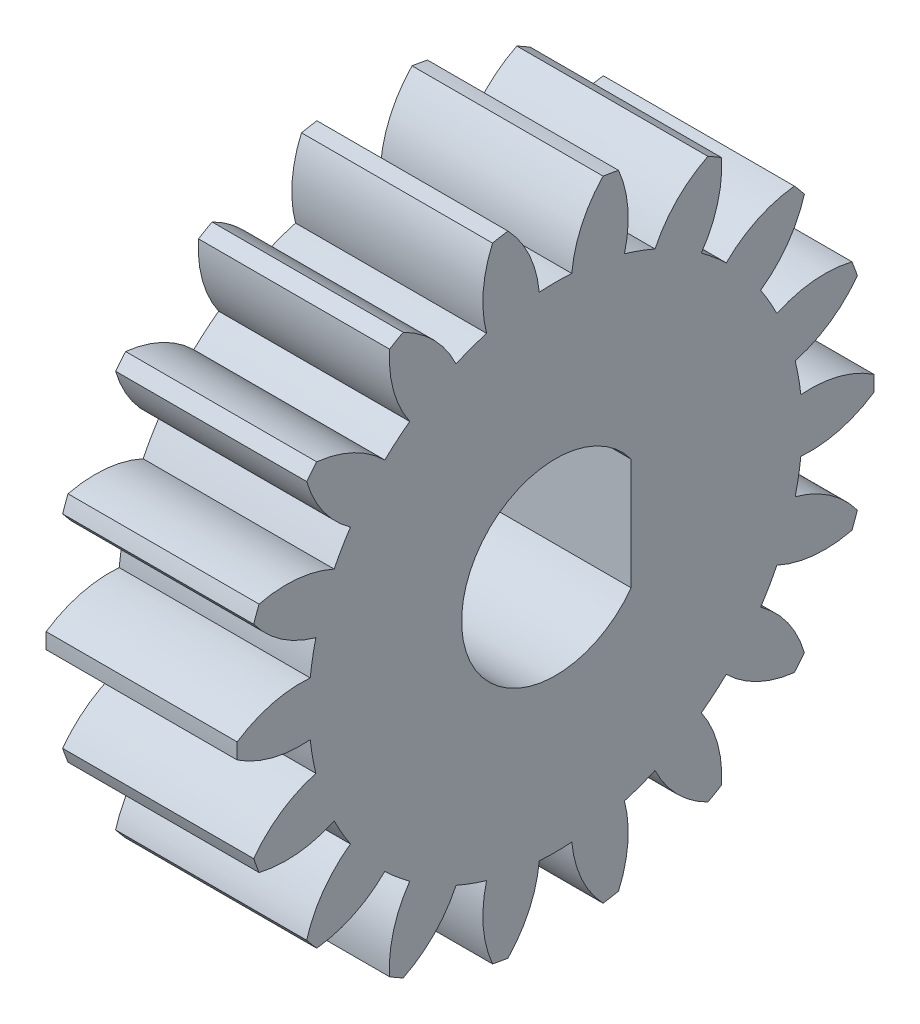
SolidWorks part; units mm, degrees
ref_plane "Plane1" through (0, 0, 0) normal (0, 0, 1) x (1, 0, 0)
ref_plane "Plane2" through (0, 0, 0) normal (0, 1, 0) x (1, 0, 0)
ref_plane "Plane3" through (0, 0, 0) normal (1, 0, 0) x (0, 0, -1)
sketch "HoldingSke" plane through (0, 0, 0) normal (0, 1, 0) x (1, 0, 0)
  line L0 (0, 0) -> (0.9511, -0.309)
  line L1 (-15, 0) -> (100, 0) construction
  line L2 (0, 0) -> (-2.1039, 2.3779)
  line L3 (0, 0) -> (-11.863, 4.5341)
  line L4 (0, 0) -> (8.2133, 2.6687)
  line L5 (0, 0) -> (-46.8476, -17.4728)
  line L6 (0, 0) -> (-4.9738, -3.3558)
  line L7 (-2.1039, 2.3779) -> (8.6586, 51.206)
  line L8 (-76.2, 54.61) -> (-75.2, 54.61)
  line L9 (-71.009, 38.7566) -> (-53.1078, 45.2721)
  line L10 (-76.2, 71.12) -> (104.1128, 71.12)
  line L11 (0, 0) -> (-6, 0)
  line L12 (-76.2, 101.6) -> (-76.162, 101.6)
  line L13 (24.9733, 27.94) -> (52.9518, 28.4284)
  line L14 (24.9733, 27.94) -> (24.9743, 27.94)
  line L15 (24.9733, 27.94) -> (100.4006, 29.5858)
  line L16 (-63.627, -1) -> (-12.827, -1)
  circle A0 centre (0, 0) radius 3
  circle A1 centre (0, 0) radius 7.749
  circle A2 centre (0, 0) radius 37.5
  circle A3 centre (0, 0) radius 3
  dimension "MHD" = 15.498
  dimension "Hub_dia" = 75
  dimension "Bore" = 6
  dimension "MBD" = 6
  dimension "Num_teeth" = 18
  dimension "Pitch" = 1
  dimension "Overall_len" = 50
  dimension "Show_teeth" = 18
  dimension "Thickness" = 6
  dimension "OAL" = 50.0002
  dimension "T_dim" = 1
  dimension "Ap" = 20
  dimension "H" = 19.05
  dimension "Pitch_radius" = 180.3128
  dimension "Width" = 6
  dimension "Backlash" = 0.038
  dimension "Addendum_fac" = 1
  dimension "Dedendum_fac" = 1.25
  dimension "Clearance_fac" = 0.25
  dimension "Dedendum_add" = 0.001
  dimension "Module" = 1
sketch "BasProSke" plane through (0, 0, 0) normal (0, 1, 0) x (1, 0, 0)
  line L0 (-10, 0) -> (60, 0) construction
  line L1 (0, 0) -> (0, 10)
  line L2 (0, 0) -> (6, 0)
  line L3 (6, 0) -> (6, 10)
  line L4 (6, 10) -> (0, 10)
  dimension "Thickness" = 6
  dimension "Diameter" = 20
revolve "Base-Revolve" add sketch "BasProSke" angle 360 about L0
sketch "TooCutSke" plane through (0, 0, 0) normal (1, 0, 0) x (0, 0, -1)
  line L1 (0, 0) -> (0, 107) construction
  line L2 (0, 0) -> (-0.8509, 8.9597) construction
  line L3 (0, 0) -> (-3.1157, 17.6701) construction
  line L4 (-0.8509, 8.9597) -> (-1.5579, 8.835) construction
  arc A0 (0.5106, 7.7322) -> (-0.5106, 7.7322) centre (0, 0) ccw
  arc A1 (1.5152, 9.9102) -> (-1.5152, 9.9102) centre (0, 0) ccw
  circle A2 centre (0, 0) radius 9 construction
  circle A3 centre (0, 0) radius 8.4572 construction
  arc A4 (-0.5106, 7.7322) -> (-1.5152, 9.9102) centre (-4.0952, 7.3996) ccw
  arc A5 (1.5152, 9.9102) -> (0.5106, 7.7322) centre (4.0952, 7.3996) ccw
  dimension "Root_dia" = 15.498
  dimension "Overcut_dia" = 20.0508
  dimension "Pitch_dia" = 18
  dimension "Base_dia" = 16.9145
  dimension "Flank_rad" = 3.6
  dimension "Half_ang" = 10
  dimension "Half_CT" = 0.7179
extrude "ToothCut" cut sketch "TooCutSke" along normal through all
fillet "Breaks" [suppressed] radius 0.02
fillet "RootFillets" [suppressed] radius 0.251
pattern_circular "TeethCuts" count 18 every 20 about axis through (-10, 0, 0) along (1, 0, 0) of "ToothCut", "RootFillets", "Breaks"
sketch "HubNeaOneSke" plane through (0, 0, 0) normal (-1, 0, 0) x (0, 0, 1)
  circle A0 centre (0, 0) radius 7.749
  dimension "Diameter" = 15.498
extrude "HubNearOne" [suppressed] add sketch "HubNeaOneSke" along normal blind 44.0002
sketch "HubNeaBotSke" plane through (0, 0, 0) normal (-1, 0, 0) x (0, 0, 1)
  circle A0 centre (0, 0) radius 7.749
  dimension "Diameter" = 15.498
extrude "HubNearBoth" [suppressed] add sketch "HubNeaBotSke" along normal blind 22.0001
ref_plane "FarPln" through (6, 0, 0) normal (1, 0, 0) x (0, 0, -1)
sketch "HubFarSke" plane through (6, 0, 0) normal (1, 0, 0) x (0, 0, -1)
  circle A0 centre (0, 0) radius 7.749
  dimension "Diameter" = 15.498
extrude "HubFar" [suppressed] add sketch "HubFarSke" along normal blind 22.0001
sketch "KeySke" plane through (0, 0, 0) normal (1, 0, 0) x (0, 0, -1)
  line L0 (-1, 0) -> (-1, 4)
  line L1 (-1, 4) -> (1, 4)
  line L2 (1, 4) -> (1, 0)
  line L3 (0, 0) -> (0, 34) construction
  line L4 (-1, 0) -> (1, 0)
  dimension "Offset" = 4
  dimension "Width" = 2
extrude "Keyway" [suppressed] cut sketch "KeySke" along normal mid plane 100.0003
pattern_circular "Keyway2" [suppressed] count 2 every 90 about axis through (-10, 0, 0) along (1, 0, 0)
sketch "Sketch1" plane through (6, 0, 0) normal (1, 0, 0) x (0, 0, -1)
  line L0 (2.3749, 1.75) -> (2.3749, -1.75)
  arc A0 (2.3749, 1.75) -> (2.3749, -1.75) centre (0, 0) ccw
  dimension "D1" = 5.9
  dimension "D2" = 3.5
extrude "Cut-Extrude1" cut sketch "Sketch1" against normal through all
equation "' \"Module@HoldingSke\" = 6.35"
equation "' \"Num_teeth@HoldingSke\" = 12"
equation "' \"Ap@HoldingSke\" =  20"
equation "' \"Ap@HoldingSke\" = 20"
equation "' \"Width@HoldingSke\" = 0.5 * 25.4"
equation "' \"Hub_dia@HoldingSke\"= 1 * 25.4"
equation "' \"Hub_dia@HoldingSke\" = 1 * 25.4"
equation "' \"Overall_len@HoldingSke\" = 1.0 * 25.4"
equation "' \"T_dim@HoldingSke\" = 0.1 * 25.4"
equation "' \"Width@KeySke\" = 0.25 * 25.4"
equation "' \"Show_teeth@HoldingSke\" = 13"
equation "' \"Backlash@HoldingSke\" = 0.009 * 25.4"
equation "' \"Addendum_fac@HoldingSke\" = 1.0"
equation "' \"Dedendum_fac@HoldingSke\" = 1.25"
equation "' \"Dedendum_add@HoldingSke\" = 0.00005 * 25.4"
equation "' \"Clearance_fac@HoldingSke\" = 0.25"
equation "\"Pitch@HoldingSke\" = 1 / \"Module@HoldingSke\""
equation "\"Overcut_dia@TooCutSke\" = (\"Num_teeth@HoldingSke\" + 2 * \"Addendum_fac@HoldingSke\") / \"Pitch@HoldingSke\" + 0.002 * 25.4"
equation "\"Pitch_dia@TooCutSke\" = \"Num_teeth@HoldingSke\" / \"Pitch@HoldingSke\""
equation "\"Base_dia@TooCutSke\" = \"Num_teeth@HoldingSke\" / \"Pitch@HoldingSke\" * cos((\"Ap@HoldingSke\"  * 3.14159265 / 180))"
equation "\"Root_dia@TooCutSke\" = (\"Num_teeth@HoldingSke\" + 2) / \"Pitch@HoldingSke\" - 2 * (\"Addendum_fac@HoldingSke\" + \"Dedendum_fac@HoldingSke\") / \"Pitch@HoldingSke\" - \"Dedendum_add@HoldingSke\" * 2"
equation "\"Half_ang@TooCutSke\" = 180 / \"Num_teeth@HoldingSke\""
equation "\"Half_CT@TooCutSke\" = \"Num_teeth@HoldingSke\" / \"Pitch@HoldingSke\" * sin((3.14159265 / 2 / \"Num_teeth@HoldingSke\")) / 2 - 7 * \"Backlash@HoldingSke\" / 4"
equation "\"Flank_rad@TooCutSke\" = \"Num_teeth@HoldingSke\" / \"Pitch@HoldingSke\" / 5"
equation "\"Radius@RootFillets\" = \"Clearance_fac@HoldingSke\" / \"Pitch@HoldingSke\" + \"Dedendum_add@HoldingSke\""
equation "\"Break_rad@Breaks\" = 0.02 / \"Pitch@HoldingSke\""
equation "\"Thickness@HoldingSke\" = \"Width@HoldingSke\""
equation "\"OAL@HoldingSke\" = \"Thickness@HoldingSke\""
equation "\"MHD@HoldingSke\" = (\"Num_teeth@HoldingSke\" + 2) / \"Pitch@HoldingSke\" - 2 * (\"Addendum_fac@HoldingSke\" + \"Dedendum_fac@HoldingSke\")  / \"Pitch@HoldingSke\" - \"Dedendum_add@HoldingSke\" * 2"
equation "\"MBD@HoldingSke\" = (\"Num_teeth@HoldingSke\" + 2) / \"Pitch@HoldingSke\" - 2 * (\"Addendum_fac@HoldingSke\" + \"Dedendum_fac@HoldingSke\")  / \"Pitch@HoldingSke\" - \"Dedendum_add@HoldingSke\" * 2 - 0.002 * 25.4"
equation "\"MHD@HoldingSke\" = ((sgn( \"MHD@HoldingSke\" - \"Hub_dia@HoldingSke\" )-1)*( \"MHD@HoldingSke\" - \"Hub_dia@HoldingSke\" ))/-2+ \"Hub_dia@HoldingSke\""
equation "\"MBD@HoldingSke\" = ((sgn( \"MBD@HoldingSke\" - \"Bore@HoldingSke\" )-1)*( \"MBD@HoldingSke\" - \"Bore@HoldingSke\" ))/-2+ \"Bore@HoldingSke\""
equation "\"OAL@HoldingSke\" = ((sgn( \"OAL@HoldingSke\" - \"Overall_len@HoldingSke\" )+1)*( \"OAL@HoldingSke\" - \"Overall_len@HoldingSke\" ))/2 + \"Overall_len@HoldingSke\" + 0.000002 * 25.4"
equation "\"Num_teeth@TeethCuts\" = int( \"Show_teeth@HoldingSke\" ) + 1"
equation "\"Num_teeth@TeethCuts\" = ((sgn( \"Num_teeth@TeethCuts\" - \"Num_teeth@HoldingSke\" )-1)*( \"Num_teeth@TeethCuts\" - \"Num_teeth@HoldingSke\" ))/-2+ \"Num_teeth@HoldingSke\""
equation "\"Num_teeth@TeethCuts\" = ((sgn( \"Num_teeth@TeethCuts\" - 2.0)+1)*( \"Num_teeth@TeethCuts\" - 2.0))/2 +2.0"
equation "\"Angle@TeethCuts\" = 360.0 / \"Num_teeth@HoldingSke\""
equation "\"Diameter@BasProSke\" = (\"Num_teeth@HoldingSke\" + 2 * \"Addendum_fac@HoldingSke\") / \"Pitch@HoldingSke\""
equation "\"Thickness@BasProSke\"  = \"Thickness@HoldingSke\""
equation "' \"Fillet_rad@BasProSke\" =  \"Thickness@HoldingSke\" * 0.05"
equation "' \"Fillet_rad@BasProSke\" = \"Thickness@HoldingSke\" * 0.05"
equation "\"MHD@HoldingSke\" = ((sgn( \"MHD@HoldingSke\" - \"Root_dia@TooCutSke\" )-1)*( \"MHD@HoldingSke\" - \"Root_dia@TooCutSke\" ))/-2+ \"Root_dia@TooCutSke\""
equation "\"Diameter@HubNeaOneSke\" = \"MHD@HoldingSke\""
equation "\"Length@HubNearOne\" = \"OAL@HoldingSke\" - \"Thickness@BasProSke\""
equation "\"Diameter@HubNeaBotSke\" = \"MHD@HoldingSke\""
equation "\"Length@HubNearBoth\" = ( \"OAL@HoldingSke\" - \"Thickness@BasProSke\" ) / 2.0"
equation "\"Thickness@FarPln\" = \"Thickness@BasProSke\""
equation "\"Diameter@HubFarSke\" = \"MHD@HoldingSke\""
equation "\"Length@HubFar\" = ( \"OAL@HoldingSke\" - \"Thickness@BasProSke\" ) / 2.0"
equation "\"D1@Keyway\" = \"OAL@HoldingSke\" * 2.0"
equation "\"Offset@KeySke\" = \"T_dim@HoldingSke\" + \"MBD@HoldingSke\" / 2.0"
